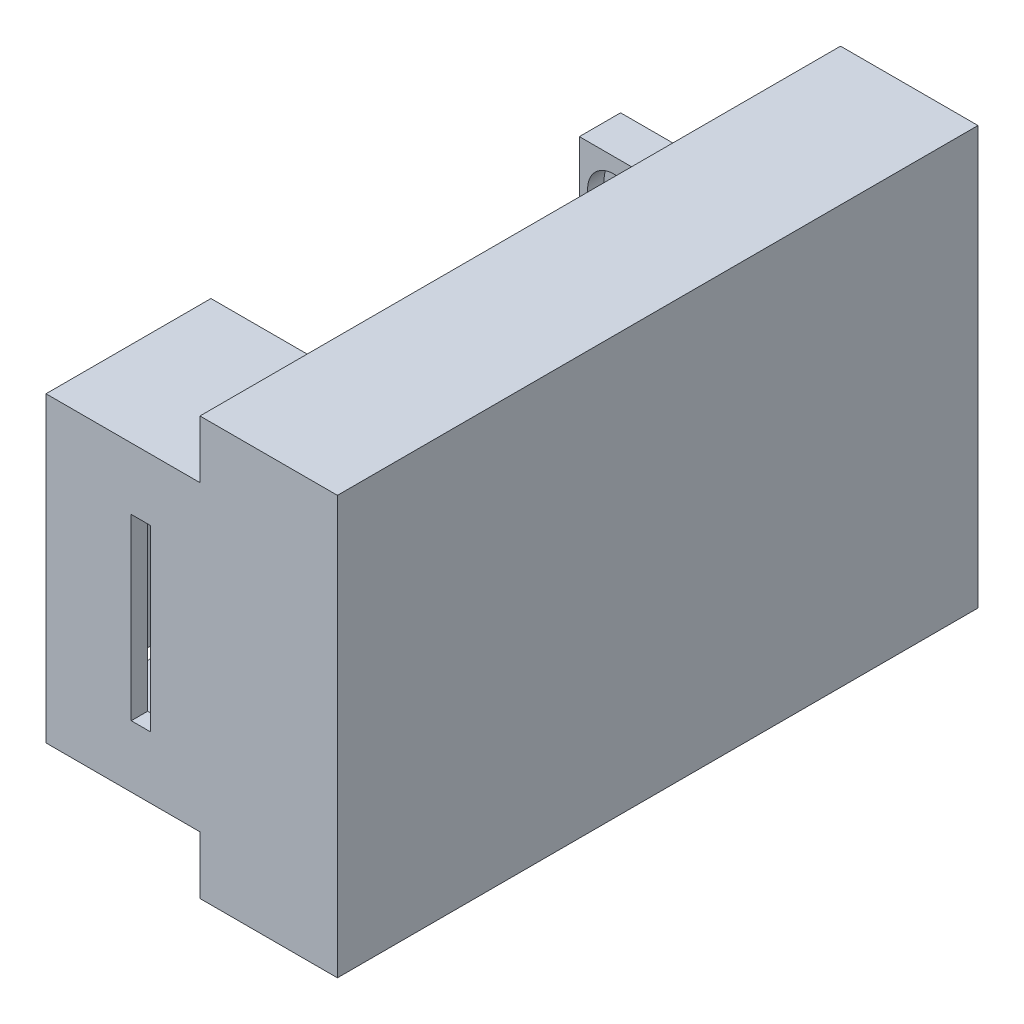
SolidWorks part; units mm, degrees
other "Markup1"
sketch "Sketch9" plane through (0, -76, -97) normal (-0.6794, -0.7318, -0.0542) x (-0.0328, -0.0434, 0.9985)
other "Markup2"
sketch "Sketch23" plane through (-80, -76, -97) normal (-0.5561, -0.0012, -0.8311) x (0.0765, -0.9958, -0.0497)
other "Markup3"
sketch "Sketch28" plane through (-80, -76, -97) normal (-0.5841, -0.0425, -0.8106) x (0.093, -0.9956, -0.0148)
other "Markup4"
sketch "Sketch31" plane through (-80, -76, -97) normal (-0.9992, -0.0096, -0.0401) x (-0.0401, 0.0073, 0.9992)
other "Markup5"
sketch "Sketch35" plane through (-80, -76, 139) normal (-0.1905, -0.96, 0.2053) x (0.1688, 0.174, 0.9702)
ref_plane "Front Plane" through (0, 0, 0) normal (0, 0, 1) x (1, 0, 0)
ref_plane "Top Plane" through (0, 0, 0) normal (0, 1, 0) x (1, 0, 0)
ref_plane "Right Plane" through (0, 0, 0) normal (1, 0, 0) x (0, 0, -1)
sketch "Sketch1" plane through (0, 0, 0) normal (1, 0, 0) x (0, 0, -1)
  line L1 (-119, 76) -> (119, 76)
  line L2 (-119, 76) -> (-119, -76)
  line L3 (-119, -76) -> (119, -76)
  line L4 (119, 76) -> (119, -76)
  line L5 (-119, 76) -> (119, -76) construction
  line L6 (-119, -76) -> (119, 76) construction
  line L7 (79, -61) -> (-79, -61)
  line L8 (79, -61) -> (79, 61)
  line L9 (79, 61) -> (-79, 61)
  line L10 (-79, -61) -> (-79, 61)
  line L11 (79, -61) -> (-79, 61) construction
  line L12 (79, 61) -> (-79, -61) construction
  point P0 (0, 0)
  point P5 (0, 0)
  dimension "D1" = 238
  dimension "D2" = 152
  dimension "D3" = 40
  dimension "D4" = 15
extrude "Boss-Extrude1" add sketch "Sketch1" along normal blind 50
ref_plane "Plane1" through (50, -61, 79) normal (0, -1, 0) x (-1, 0, 0)
sketch "Sketch4" plane through (50, 0, 0) normal (1, 0, 0) x (0, 0, -1)
  line L0 (-79, 61) -> (-79, -61) construction
  line L1 (79, -61) -> (-79, -61)
  line L2 (79, -61) -> (79, 61)
  line L3 (79, 61) -> (-79, 61)
  line L4 (-79, -61) -> (-79, 61)
  line L5 (79, -61) -> (-79, 61) construction
  line L6 (79, 61) -> (-79, -61) construction
  line L7 (79, 61) -> (-79, 61) construction
  point P0 (0, 0)
extrude "Boss-Extrude2" add sketch "Sketch4" against normal blind 10
sketch "Sketch5" plane through (0, 0, 119) normal (0, 0, 1) x (1, 0, 0)
  line L0 (5, -66) -> (5, 66)
  line L1 (5, -66) -> (13, -66)
  line L2 (5, 66) -> (13, 66)
  line L3 (13, -66) -> (13, 66)
  line L4 (5, -66) -> (13, 66) construction
  line L5 (5, 66) -> (13, -66) construction
  line L6 (50, 76) -> (0, 76) construction
  line L7 (50, -76) -> (0, -76) construction
  line L8 (0, 76) -> (0, -76) construction
  point P1 (9, 0)
  dimension "D1" = 10
  dimension "D2" = 10
  dimension "D3" = 5
  dimension "D4" = 8
extrude "Cut-Extrude1" cut sketch "Sketch5" against normal blind 204 from offset 30 offset against normal yes
sketch "Sketch8" plane through (0, 0, 0) normal (-1, 0, 0) x (0, 0, 1)
  line L0 (119, -76) -> (-119, -76) construction
  line L1 (-119, 76) -> (-94, 76)
  line L2 (-119, 76) -> (-119, -76)
  line L3 (-119, -76) -> (-94, -76)
  line L4 (-94, 76) -> (-94, -76)
  dimension "D1" = 25
extrude "Cut-Extrude3" cut sketch "Sketch8" against normal blind 50
sketch "Sketch11" plane through (0, 0, 0) normal (-1, 0, 0) x (0, 0, 1)
  line L0 (-94, -76) -> (-94, 76) construction
  line L1 (-94, 15) -> (-79, 15)
  line L2 (-94, 15) -> (-94, -15)
  line L3 (-94, -15) -> (-79, -15)
  line L4 (-79, 15) -> (-79, -15)
  line L5 (-79, -61) -> (-79, 61) construction
  line L6 (-94, 76) -> (119, 76) construction
  line L7 (119, -76) -> (-94, -76) construction
  dimension "D1" = 61
  dimension "D2" = 61
extrude "Boss-Extrude4" add sketch "Sketch11" along normal blind 75
sketch "Sketch16" plane through (-75, 0, 0) normal (-1, 0, 0) x (0, 0, 1)
  line L1 (-94, 15) -> (-79, 15)
  line L2 (-94, 15) -> (-94, -15)
  line L3 (-94, -15) -> (-79, -15)
  line L4 (-79, 15) -> (-79, -15)
extrude "Boss-Extrude6" add sketch "Sketch16" along normal blind 5
sketch "Sketch18" plane through (0, 0, -94) normal (0, 0, -1) x (-1, 0, 0)
  line L0 (-71.2187, 0) -> (106.857, 0) construction
  line L1 (-5, 66) -> (-13, 66) construction
  line L2 (-13, 71) -> (-5, 71)
  line L3 (-13, 71) -> (-13, 66)
  line L4 (-13, 66) -> (-5, 66) construction
  line L5 (-13, 66) -> (-5, 66)
  line L6 (-5, -66) -> (-5, 66) construction
  line L7 (-5, 71) -> (-5, 66)
  line L9 (-13, -66) -> (-5, -66)
  line L10 (-13, -71) -> (-13, -66)
  line L11 (-13, -71) -> (-5, -71)
  line L12 (-5, -71) -> (-5, -66)
  circle A0 centre (-9, 71) radius 4
  circle A1 centre (-9, -71) radius 4
  line M15 (-13, 66) -> (-5, 66)
  dimension "D1" = 8
  dimension "D2" = 4
  dimension "D3" = 5
  dimension "D4" = 8
  dimension "D5" = 5
  dimension "D6" = 0
extrude "Cut-Extrude8" cut sketch "Sketch18" against normal blind 7.5 contours L2 A0 | L2 A0 | A0 L3 L7 M15 | A1 L11
sketch "Sketch19" plane through (0, 0, -86.5) normal (0, 0, -1) x (-1, 0, 0)
  line L0 (-67.4628, 0) -> (105.146, 0) construction
  circle A0 centre (-9, 71) radius 2
  circle A1 centre (-9, -71) radius 2
  dimension "D1" = 4
extrude "Cut-Extrude9" cut sketch "Sketch19" against normal blind 10
sketch "Sketch20" plane through (0, 0, 119) normal (0, 0, 1) x (1, 0, 0)
  line L1 (0, 76) -> (50, 76)
  line L2 (0, 76) -> (0, -76)
  line L3 (0, -76) -> (50, -76)
  line L4 (50, 76) -> (50, -76)
extrude "Boss-Extrude7" add sketch "Sketch20" along normal blind 20
sketch "Sketch21" plane through (0, 0, 0) normal (-1, 0, 0) x (0, 0, 1)
  line L0 (-94, 76) -> (139, 76) construction
  line L1 (79, 55) -> (139, 55)
  line L2 (79, 55) -> (79, -55)
  line L3 (79, -55) -> (139, -55)
  line L4 (139, 55) -> (139, -55)
  line L6 (79, 61) -> (79, -61) construction
  line L7 (139, 76) -> (139, -76) construction
  dimension "D1" = 110
  dimension "D2" = 21
  dimension "D3" = 0
  dimension "D4" = 0
extrude "Boss-Extrude8" add sketch "Sketch21" along normal blind 56
sketch "Sketch22" plane through (0, 0, 79) normal (0, 0, -1) x (-1, 0, 0)
  line L0 (56, 55) -> (0, 55) construction
  line L1 (0, 47.5) -> (50, 47.5)
  line L2 (0, 47.5) -> (0, -47.5)
  line L3 (0, -47.5) -> (50, -47.5)
  line L4 (50, 47.5) -> (50, -47.5)
  line L5 (56, -55) -> (0, -55) construction
  line L6 (56, 55) -> (56, -55) construction
  line L7 (0, 61) -> (0, 55) construction
  dimension "D1" = 7.5
  dimension "D2" = 7.5
  dimension "D3" = 6
  dimension "D4" = 0
extrude "Cut-Extrude10" cut sketch "Sketch22" against normal blind 54
sketch "Sketch24" plane through (0, 0, 0) normal (-1, 0, 0) x (0, 0, 1)
  line L0 (139, -55) -> (139, 55) construction
  line L2 (139, 55) -> (79, 55) construction
  line L3 (79, -55) -> (139, -55) construction
  circle A0 centre (108.6, 36) radius 2.75
  circle A1 centre (108.6, -36) radius 2.75
  dimension "D1" = 5.5
  dimension "D2" = 5.5
  dimension "D5" = 19
  dimension "D3" = 72
  dimension "D4" = 30.4
  dimension "D6" = 19
extrude "Cut-Extrude11" cut sketch "Sketch24" against normal blind 40 and the other way blind 1
sketch "Sketch25" plane through (0, 0, 133) normal (0, 0, -1) x (-1, 0, 0)
  line L0 (50, 47.5) -> (0, 47.5) construction
  line L1 (18, 32.5) -> (25, 32.5)
  line L2 (18, 32.5) -> (18, -32.5)
  line L3 (18, -32.5) -> (25, -32.5)
  line L4 (25, 32.5) -> (25, -32.5)
  line L5 (0, -47.5) -> (50, -47.5) construction
  line L6 (0, 47.5) -> (0, -47.5) construction
  line L7 (50, -47.5) -> (50, 47.5) construction
  dimension "D1" = 15
  dimension "D2" = 15
  dimension "D3" = 18
  dimension "D4" = 25
extrude "Cut-Extrude12" cut sketch "Sketch25" against normal blind 12
sketch "Sketch26" plane through (0, 0, 0) normal (-1, 0, 0) x (0, 0, 1)
  line L0 (79, 61) -> (79, -61) construction
  line L1 (79, 47.5) -> (131.5, 47.5)
  line L2 (79, 47.5) -> (79, 41.5)
  line L3 (79, 41.5) -> (131.5, 41.5)
  line L4 (131.5, 47.5) -> (131.5, 41.5)
  line L5 (139, 55) -> (79, 55) construction
  line L6 (139, -55) -> (139, 55) construction
  line L7 (-36.1574, 0) -> (182.6959, 0) construction
  line L8 (79, -47.5) -> (79, -41.5)
  line L9 (131.5, -47.5) -> (131.5, -41.5)
  line L10 (79, -41.5) -> (131.5, -41.5)
  line L11 (79, -47.5) -> (131.5, -47.5)
  dimension "D1" = 7.5
  dimension "D2" = 7.5
  dimension "D3" = 6
extrude "Cut-Extrude13" cut sketch "Sketch26" against normal blind 40
sketch "Sketch27" plane through (13, 0, 0) normal (-1, 0, 0) x (0, 0, 1)
  line L0 (79, 55) -> (79, -55) construction
  line L1 (79, 41.5) -> (94, 41.5)
  line L2 (79, 41.5) -> (79, -41.5)
  line L3 (79, -41.5) -> (94, -41.5)
  line L4 (94, 41.5) -> (94, -41.5)
  line L5 (139, 55) -> (79, 55) construction
  dimension "D1" = 83
  dimension "D2" = 13.5
  dimension "D3" = 15
extrude "Cut-Extrude14" cut sketch "Sketch27" against normal blind 30
sketch "Sketch29" plane through (0, 0, -79) normal (0, 0, 1) x (1, 0, 0)
  line L0 (-80, 15) -> (0, 15) construction
  line L3 (-80, -15) -> (-80, 15) construction
  circle A0 centre (-67.5, 0) radius 9.5
  dimension "D1" = 19
  dimension "D2" = 15
  dimension "D3" = 12.5
extrude "Cut-Extrude15" cut sketch "Sketch29" against normal blind 6
sketch "Sketch30" plane through (-56, 0, 0) normal (-1, 0, 0) x (0, 0, 1)
  line L0 (79, 41.5) -> (79, -41.5) construction
  line L1 (79, 55) -> (79, -55) construction
  line L2 (79, -55) -> (139, -55) construction
  circle A2 centre (82.5, 8) radius 2.5
  circle A3 centre (107.5, 8) radius 2.5
  circle A4 centre (82.5, 43) radius 2.5
  circle A5 centre (107.5, 43) radius 2.5
  point P12 (0, 0)
  dimension "D1" = 5
  dimension "D2" = 5
  dimension "D3" = 5
  dimension "D4" = 5
  dimension "D5" = 3.5
  dimension "D6" = 35
  dimension "D7" = 25
  dimension "D8" = 35
  dimension "D9" = 3.5
  dimension "D10" = 63
  dimension "D11" = 63
  dimension "D12" = 25
extrude "Cut-Extrude16" cut sketch "Sketch30" against normal blind 6
sketch "Sketch34" plane through (-56, 0, 0) normal (-1, 0, 0) x (0, 0, 1)
  line L0 (79, -55) -> (139, -55) construction
  line L1 (86.5, -37.5) -> (131.5, -37.5)
  line L2 (86.5, -37.5) -> (86.5, -47.5)
  line L3 (86.5, -47.5) -> (131.5, -47.5)
  line L4 (131.5, -37.5) -> (131.5, -47.5)
  line L5 (139, -55) -> (139, 55) construction
  line L6 (79, 55) -> (79, -55) construction
  dimension "D1" = 7.5
  dimension "D2" = 7.5
  dimension "D3" = 7.5
  dimension "D4" = 10
extrude "Cut-Extrude17" cut sketch "Sketch34" against normal blind 10
